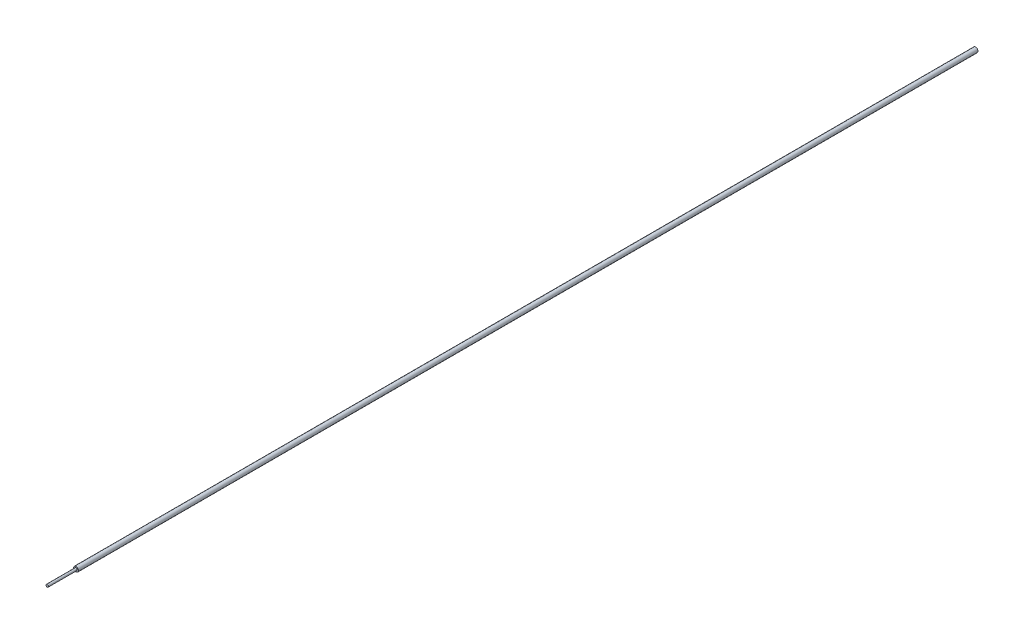
SolidWorks part; units mm, degrees
ref_plane "Front Plane" through (0, 0, 0) normal (0, 0, 1) x (1, 0, 0)
ref_plane "Top Plane" through (0, 0, 0) normal (0, 1, 0) x (1, 0, 0)
ref_plane "Right Plane" through (0, 0, 0) normal (1, 0, 0) x (0, 0, -1)
sketch "Sketch1" plane through (0, 0, 0) normal (0, 1, 0) x (1, 0, 0)
  line L0 (0, 0) -> (0, 387)
  line L1 (0, 0) -> (0.5, 0)
  line L2 (0.5, 0) -> (0.5, 12)
  line L3 (0.5, 12) -> (1, 12)
  line L4 (1, 12) -> (1, 387)
  line L5 (0, 0) -> (0, -50.3051) construction
  line L6 (0, 387) -> (1, 387)
  dimension "D1" = 1
  dimension "D2" = 2
  dimension "D3" = 12
  dimension "D4" = 375
revolve "Revolve1" add sketch "Sketch1" angle 360 about L5
